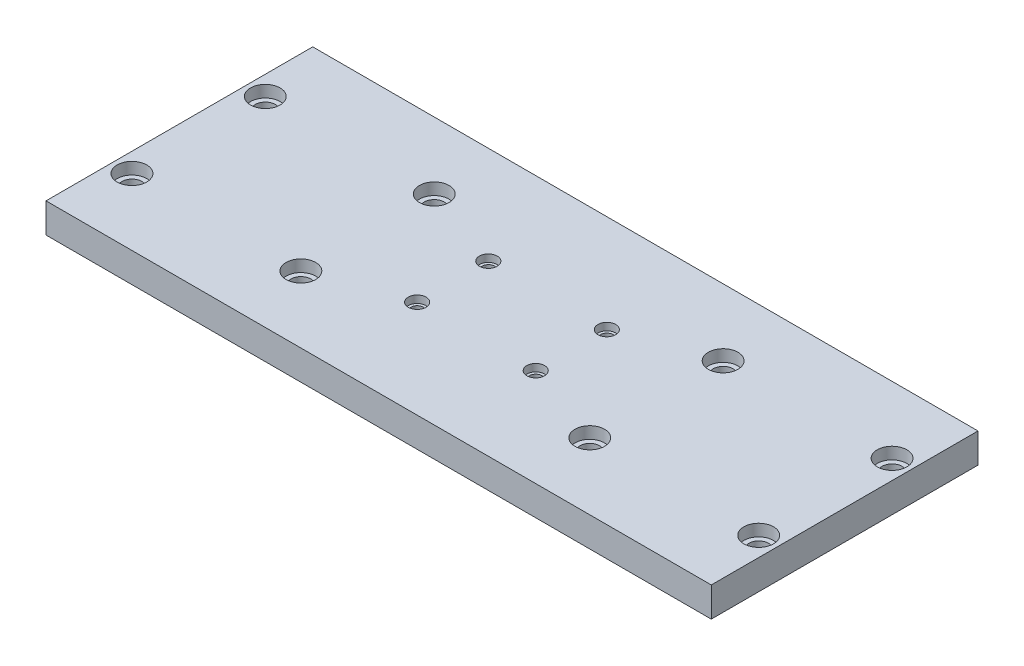
SolidWorks part; units mm, degrees
material "Aleación 2018"
ref_plane "Alzado" through (0, 0, 0) normal (0, 0, 1) x (1, 0, 0)
ref_plane "Planta" through (0, 0, 0) normal (0, 1, 0) x (1, 0, 0)
ref_plane "Vista lateral" through (0, 0, 0) normal (1, 0, 0) x (0, 0, -1)
sketch "Croquis1" plane through (0, 0, 0) normal (0, 1, 0) x (1, 0, 0)
  line L1 (-112.24, -45) -> (112.24, -45)
  line L2 (-112.24, -45) -> (-112.24, 45)
  line L3 (-112.24, 45) -> (112.24, 45)
  line L4 (112.24, -45) -> (112.24, 45)
  line L5 (-112.24, -45) -> (112.24, 45) construction
  line L6 (-112.24, 45) -> (112.24, -45) construction
  point P0 (0, 0)
  dimension "D1" = 90
  dimension "D2" = 224.48
extrude "Saliente-Extruir1" add sketch "Croquis1" along normal blind 10
sketch "Croquis2" plane through (0, 0, 0) normal (0, 1, 0) x (1, 0, 0)
  line L0 (-112.24, 45) -> (-105.74, 45) construction
  line L1 (112.24, 45) -> (-112.24, 45) construction
  line L2 (-105.74, 45) -> (-105.74, 22.5) construction
  line L3 (-105.74, -45) -> (-105.74, -22.5) construction
  line L4 (-112.24, -45) -> (112.24, -45) construction
  line L5 (112.24, 22.5) -> (105.74, 22.5) construction
  line L6 (112.24, -45) -> (112.24, 45) construction
  line L7 (112.24, -22.5) -> (105.74, -22.5) construction
  circle A0 centre (-105.74, 22.5) radius 3.35
  circle A1 centre (105.74, 22.5) radius 3.35
  circle A2 centre (105.74, -22.5) radius 3.35
  circle A3 centre (-105.74, -22.5) radius 3.35
  dimension "D6" = 6.7
  dimension "D7" = 6.7
  dimension "D8" = 6.7
  dimension "D9" = 6.7
  dimension "D1" = 6.5
  dimension "D2" = 22.5
  dimension "D3" = 22.5
  dimension "D4" = 6.5
  dimension "D5" = 6.5
extrude "Cortar-Extruir1" cut sketch "Croquis2" along normal through all
sketch "Croquis22" plane through (0, 0, 0) normal (0, 1, 0) x (1, 0, 0)
  line L7 (-20, -12) -> (20, 12) construction
  line L8 (-20, 12) -> (20, -12) construction
  circle A0 centre (20, 12) radius 2.1
  circle A1 centre (-20, 12) radius 2.1
  circle A2 centre (-20, -12) radius 2.1
  circle A3 centre (20, -12) radius 2.1
  point P8 (0, 0)
  dimension "D3" = 4.2
  dimension "D4" = 4.2
  dimension "D5" = 4.2
  dimension "D6" = 4.2
  dimension "D1" = 24
  dimension "D2" = 40
extrude "Cortar-Extruir3" cut sketch "Croquis22" along normal through all
ref_plane "Plano9" through (0, 10, 0) normal (0, 1, 0) x (1, 0, 0)
sketch "Croquis25" plane through (0, 10, 0) normal (0, 1, 0) x (1, 0, 0)
  circle A0 centre (-105.74, 22.5) radius 5
  circle A1 centre (-105.74, -22.5) radius 5
  circle A2 centre (105.74, 22.5) radius 5
  circle A3 centre (105.74, -22.5) radius 5
  dimension "D1" = 10
  dimension "D2" = 10
  dimension "D3" = 10
  dimension "D4" = 10
extrude "Cortar-Extruir4" cut sketch "Croquis25" against normal blind 4
sketch "Croquis26" plane through (0, 10, 0) normal (0, 1, 0) x (1, 0, 0)
  circle A0 centre (-20, 12) radius 3
  circle A1 centre (20, 12) radius 3
  circle A2 centre (20, -12) radius 3
  circle A3 centre (-20, -12) radius 3
  dimension "D1" = 6
  dimension "D2" = 6
  dimension "D3" = 6
  dimension "D4" = 6
extrude "Cortar-Extruir5" cut sketch "Croquis26" against normal blind 2.5
sketch "Croquis27" plane through (0, 10, 0) normal (0, 1, 0) x (1, 0, 0)
  line L0 (-105.74, 22.5) -> (-48.74, 22.5) construction
  line L1 (-105.74, -22.5) -> (-48.74, -22.5) construction
  line L2 (105.74, 22.5) -> (48.74, 22.5) construction
  line L3 (105.74, -22.5) -> (48.74, -22.5) construction
  circle A0 centre (-48.74, 22.5) radius 3.35
  circle A1 centre (48.74, 22.5) radius 3.35
  circle A2 centre (48.74, -22.5) radius 3.35
  circle A3 centre (-48.74, -22.5) radius 3.35
  dimension "D3" = 6.7
  dimension "D4" = 6.7
  dimension "D5" = 6.7
  dimension "D6" = 6.7
  dimension "D1" = 57
  dimension "D2" = 57
  dimension "D7" = 57
  dimension "D8" = 57
extrude "Cortar-Extruir6" cut sketch "Croquis27" against normal through all
sketch "Croquis28" plane through (0, 10, 0) normal (0, 1, 0) x (1, 0, 0)
  circle A0 centre (-48.74, 22.5) radius 5
  circle A1 centre (-48.74, -22.5) radius 5
  circle A2 centre (48.74, -22.5) radius 5
  circle A3 centre (48.74, 22.5) radius 5
  dimension "D1" = 10
  dimension "D2" = 10
  dimension "D3" = 10
  dimension "D4" = 10
extrude "Cortar-Extruir7" cut sketch "Croquis28" against normal blind 4
